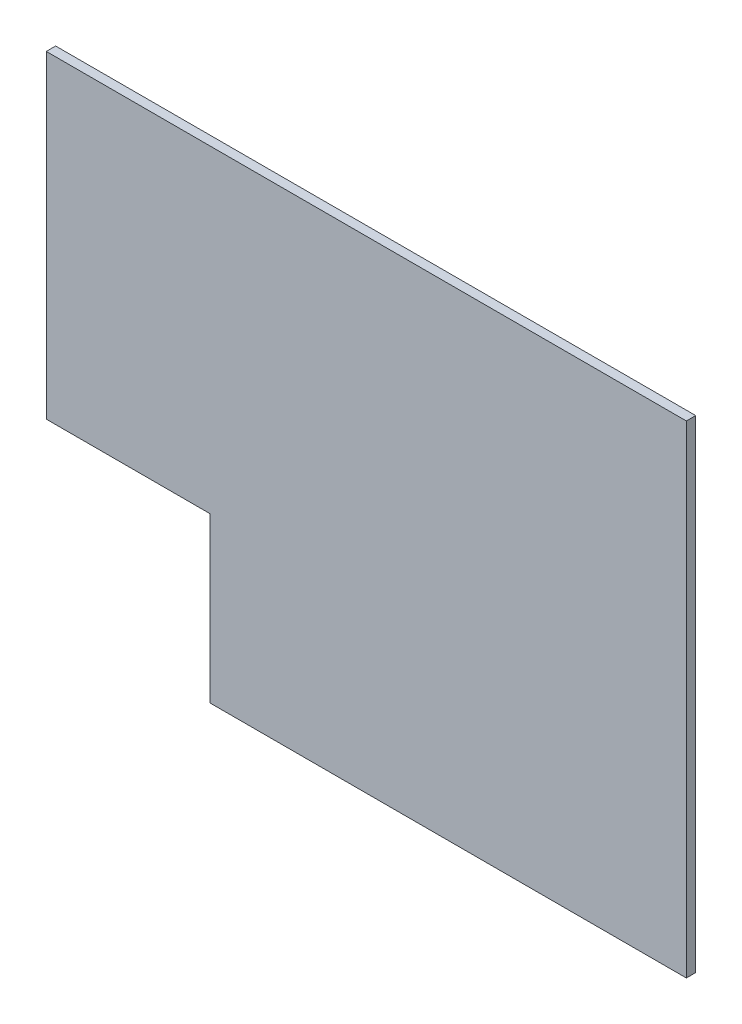
SolidWorks part; units mm, degrees
ref_plane "Plan de face" through (0, 0, 0) normal (0, 0, 1) x (1, 0, 0)
ref_plane "Plan de dessus" through (0, 0, 0) normal (0, 1, 0) x (1, 0, 0)
ref_plane "Plan de droite" through (0, 0, 0) normal (1, 0, 0) x (0, 0, -1)
sketch "Esquisse1" plane through (0, 0, 0) normal (0, 0, 1) x (1, 0, 0)
  line L0 (46.9618, -31.9972) -> (46.9618, 20.5028)
  line L1 (-5.5382, 122.5028) -> (-5.5382, 20.5028)
  line L2 (46.9618, -31.9972) -> (199.4618, -31.9972)
  line L3 (-5.5382, 122.5028) -> (199.4618, 122.5028)
  line L4 (199.4618, -31.9972) -> (199.4618, 122.5028)
  line L5 (46.9618, 20.5028) -> (-5.5382, 20.5028)
  dimension "D1" = 154.5
  dimension "D2" = 205
  dimension "D3" = 52.5
  dimension "D4" = 52.5
extrude "Boss.-Extru.1" add sketch "Esquisse1" along normal blind 3
